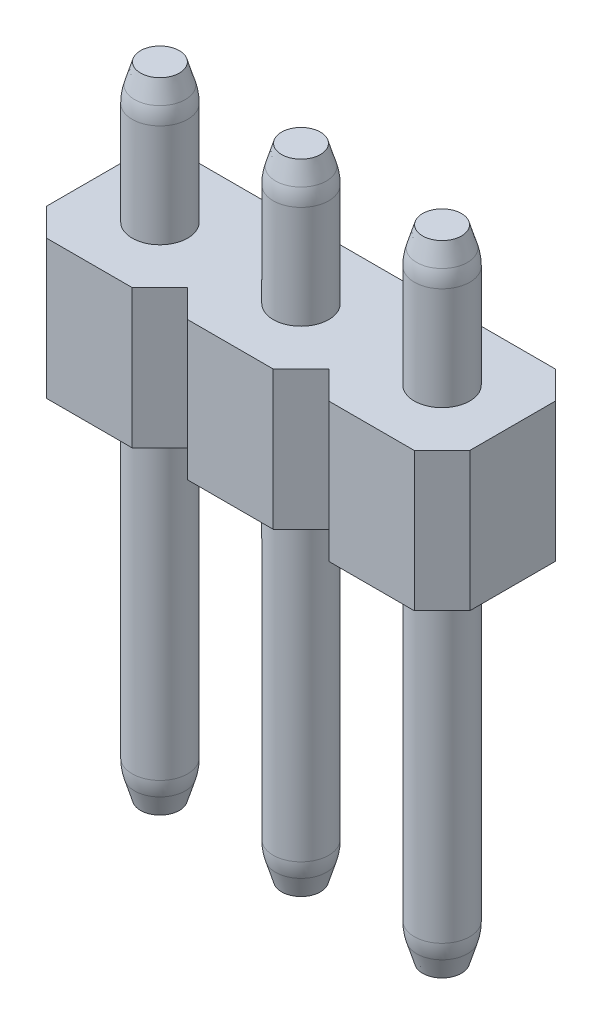
SolidWorks part; units mm, degrees
material "Brass"
ref_plane "Front Plane" through (0, 0, 0) normal (0, 0, 1) x (1, 0, 0)
ref_plane "Top Plane" through (0, 0, 0) normal (0, 1, 0) x (1, 0, 0)
ref_plane "Right Plane" through (0, 0, 0) normal (1, 0, 0) x (0, 0, -1)
sketch "Sketch1" plane through (0, 0, 0) normal (0, 1, 0) x (1, 0, 0)
  line L0 (0, 0) -> (2.54, 0) construction
  circle A0 centre (0, 0) radius 0.5
  circle A1 centre (2.54, 0) radius 0.5
  circle A2 centre (5.08, 0) radius 0.5
  circle A3 centre (7.62, 0) radius 0.5
  circle A4 centre (10.16, 0) radius 0.5
  circle A5 centre (12.7, 0) radius 0.5
  circle A6 centre (15.24, 0) radius 0.5
  circle A7 centre (17.78, 0) radius 0.5
  circle A8 centre (20.32, 0) radius 0.5
  circle A9 centre (22.86, 0) radius 0.5
  circle A10 centre (25.4, 0) radius 0.5
  circle A11 centre (27.94, 0) radius 0.5
  circle A12 centre (30.48, 0) radius 0.5
  circle A13 centre (33.02, 0) radius 0.5
  circle A14 centre (35.56, 0) radius 0.5
  circle A15 centre (38.1, 0) radius 0.5
  dimension "D1" = 1
  dimension "D3" = 2.54
  dimension "D2" = 16
extrude "Boss-Extrude1" add sketch "Sketch1" along normal blind 11.5
ref_plane "Plane1" through (0, 6.5, 0) normal (0, 1, 0) x (1, 0, 0)
sketch "Sketch2" plane through (0, 6.5, 0) normal (0, 1, 0) x (1, 0, 0)
  line L0 (-1.27, 0.77) -> (-0.77, 1.27)
  line L1 (-0.77, -1.27) -> (0.77, -1.27)
  line L2 (-1.27, -0.77) -> (-1.27, 0.77)
  line L3 (-0.77, 1.27) -> (0.77, 1.27)
  line L5 (-1.27, -1.27) -> (1.27, 1.27) construction
  line L6 (-1.27, 1.27) -> (1.27, -1.27) construction
  line L7 (0.77, 1.27) -> (1.27, 0.77)
  line L8 (0.77, -1.27) -> (1.27, -0.77)
  line L9 (-1.27, -0.77) -> (-0.77, -1.27)
  line L10 (1.27, 0.77) -> (1.77, 1.27)
  line L11 (1.77, 1.27) -> (3.31, 1.27)
  line L12 (3.31, 1.27) -> (3.81, 0.77)
  line L14 (3.31, -1.27) -> (3.81, -0.77)
  line L15 (1.77, -1.27) -> (3.31, -1.27)
  line L16 (1.27, -0.77) -> (1.77, -1.27)
  line L17 (3.81, 0.77) -> (4.31, 1.27)
  line L18 (4.31, 1.27) -> (5.85, 1.27)
  line L19 (5.85, 1.27) -> (6.35, 0.77)
  line L20 (6.35, -0.77) -> (6.35, 0.77) construction
  line L21 (5.85, -1.27) -> (6.35, -0.77)
  line L22 (4.31, -1.27) -> (5.85, -1.27)
  line L23 (3.81, -0.77) -> (4.31, -1.27)
  line L24 (6.35, 0.77) -> (6.85, 1.27)
  line L25 (6.85, 1.27) -> (8.39, 1.27)
  line L26 (8.39, 1.27) -> (8.89, 0.77)
  line L27 (8.89, -0.77) -> (8.89, 0.77) construction
  line L28 (8.39, -1.27) -> (8.89, -0.77)
  line L29 (6.85, -1.27) -> (8.39, -1.27)
  line L30 (6.35, -0.77) -> (6.85, -1.27)
  line L31 (8.89, 0.77) -> (9.39, 1.27)
  line L32 (9.39, 1.27) -> (10.93, 1.27)
  line L33 (10.93, 1.27) -> (11.43, 0.77)
  line L34 (11.43, -0.77) -> (11.43, 0.77) construction
  line L35 (10.93, -1.27) -> (11.43, -0.77)
  line L36 (9.39, -1.27) -> (10.93, -1.27)
  line L37 (8.89, -0.77) -> (9.39, -1.27)
  line L38 (11.43, 0.77) -> (11.93, 1.27)
  line L39 (11.93, 1.27) -> (13.47, 1.27)
  line L40 (13.47, 1.27) -> (13.97, 0.77)
  line L41 (13.97, -0.77) -> (13.97, 0.77) construction
  line L42 (13.47, -1.27) -> (13.97, -0.77)
  line L43 (11.93, -1.27) -> (13.47, -1.27)
  line L44 (11.43, -0.77) -> (11.93, -1.27)
  line L45 (13.97, 0.77) -> (14.47, 1.27)
  line L46 (14.47, 1.27) -> (16.01, 1.27)
  line L47 (16.01, 1.27) -> (16.51, 0.77)
  line L48 (16.51, -0.77) -> (16.51, 0.77) construction
  line L49 (16.01, -1.27) -> (16.51, -0.77)
  line L50 (14.47, -1.27) -> (16.01, -1.27)
  line L51 (13.97, -0.77) -> (14.47, -1.27)
  line L52 (16.51, 0.77) -> (17.01, 1.27)
  line L53 (17.01, 1.27) -> (18.55, 1.27)
  line L54 (18.55, 1.27) -> (19.05, 0.77)
  line L55 (19.05, -0.77) -> (19.05, 0.77) construction
  line L56 (18.55, -1.27) -> (19.05, -0.77)
  line L57 (17.01, -1.27) -> (18.55, -1.27)
  line L58 (16.51, -0.77) -> (17.01, -1.27)
  line L59 (19.05, 0.77) -> (19.55, 1.27)
  line L60 (19.55, 1.27) -> (21.09, 1.27)
  line L61 (21.09, 1.27) -> (21.59, 0.77)
  line L62 (21.59, -0.77) -> (21.59, 0.77) construction
  line L63 (21.09, -1.27) -> (21.59, -0.77)
  line L64 (19.55, -1.27) -> (21.09, -1.27)
  line L65 (19.05, -0.77) -> (19.55, -1.27)
  line L66 (21.59, 0.77) -> (22.09, 1.27)
  line L67 (22.09, 1.27) -> (23.63, 1.27)
  line L68 (23.63, 1.27) -> (24.13, 0.77)
  line L69 (24.13, -0.77) -> (24.13, 0.77) construction
  line L70 (23.63, -1.27) -> (24.13, -0.77)
  line L71 (22.09, -1.27) -> (23.63, -1.27)
  line L72 (21.59, -0.77) -> (22.09, -1.27)
  line L73 (24.13, 0.77) -> (24.63, 1.27)
  line L74 (24.63, 1.27) -> (26.17, 1.27)
  line L75 (26.17, 1.27) -> (26.67, 0.77)
  line L76 (26.67, -0.77) -> (26.67, 0.77) construction
  line L77 (26.17, -1.27) -> (26.67, -0.77)
  line L78 (24.63, -1.27) -> (26.17, -1.27)
  line L79 (24.13, -0.77) -> (24.63, -1.27)
  line L80 (26.67, 0.77) -> (27.17, 1.27)
  line L81 (27.17, 1.27) -> (28.71, 1.27)
  line L82 (28.71, 1.27) -> (29.21, 0.77)
  line L83 (29.21, -0.77) -> (29.21, 0.77) construction
  line L84 (28.71, -1.27) -> (29.21, -0.77)
  line L85 (27.17, -1.27) -> (28.71, -1.27)
  line L86 (26.67, -0.77) -> (27.17, -1.27)
  line L87 (29.21, 0.77) -> (29.71, 1.27)
  line L88 (29.71, 1.27) -> (31.25, 1.27)
  line L89 (31.25, 1.27) -> (31.75, 0.77)
  line L90 (31.75, -0.77) -> (31.75, 0.77) construction
  line L91 (31.25, -1.27) -> (31.75, -0.77)
  line L92 (29.71, -1.27) -> (31.25, -1.27)
  line L93 (29.21, -0.77) -> (29.71, -1.27)
  line L94 (31.75, 0.77) -> (32.25, 1.27)
  line L95 (32.25, 1.27) -> (33.79, 1.27)
  line L96 (33.79, 1.27) -> (34.29, 0.77)
  line L97 (34.29, -0.77) -> (34.29, 0.77) construction
  line L98 (33.79, -1.27) -> (34.29, -0.77)
  line L99 (32.25, -1.27) -> (33.79, -1.27)
  line L100 (31.75, -0.77) -> (32.25, -1.27)
  line L101 (34.29, 0.77) -> (34.79, 1.27)
  line L102 (34.79, 1.27) -> (36.33, 1.27)
  line L103 (36.33, 1.27) -> (36.83, 0.77)
  line L104 (36.83, -0.77) -> (36.83, 0.77) construction
  line L105 (36.33, -1.27) -> (36.83, -0.77)
  line L106 (34.79, -1.27) -> (36.33, -1.27)
  line L107 (34.29, -0.77) -> (34.79, -1.27)
  line L108 (36.83, 0.77) -> (37.33, 1.27)
  line L109 (37.33, 1.27) -> (38.87, 1.27)
  line L110 (38.87, 1.27) -> (39.37, 0.77)
  line L111 (39.37, -0.77) -> (39.37, 0.77)
  line L112 (38.87, -1.27) -> (39.37, -0.77)
  line L113 (37.33, -1.27) -> (38.87, -1.27)
  line L114 (36.83, -0.77) -> (37.33, -1.27)
  line L115 (-1.27, 0.77) -> (1.27, 0.77) construction
  point P0 (0, 0)
  dimension "D1" = 2.54
  dimension "D2" = 2.54
  dimension "D4" = 2.54
  dimension "D3" = 16
extrude "Boss-Extrude2" add sketch "Sketch2" along normal blind 2.5
chamfer "Chamfer1" distance 0.5 distance2 0.15 16 edges at (15.24, 11.5, 0.5) (12.7, 11.5, 0.5) (10.16, 11.5, 0.5) (7.62, 11.5, 0.5) (5.08, 11.5, 0.5) (2.54, 11.5, 0.5) (0, 11.5, 0.5) (38.1, 11.5, 0.5) (35.56, 11.5, 0.5) (33.02, 11.5, 0.5) (30.48, 11.5, 0.5) (27.94, 11.5, 0.5) (25.4, 11.5, 0.5) (22.86, 11.5, 0.5) (20.32, 11.5, 0.5) (17.78, 11.5, 0.5)
fillet "Fillet1" radius 1 16 edges at (38.1, 11, 0.5) (35.56, 11, 0.5) (33.02, 11, 0.5) (30.48, 11, 0.5) (27.94, 11, 0.5) (25.4, 11, 0.5) (22.86, 11, 0.5) (20.32, 11, 0.5) (17.78, 11, 0.5) (15.24, 11, 0.5) (12.7, 11, 0.5) (10.16, 11, 0.5) (7.62, 11, 0.5) (5.08, 11, 0.5) (2.54, 11, 0.5) (0, 11, 0.5)
chamfer "Chamfer2" distance 0.15 distance2 0.5 16 edges at (10.16, 0, 0.5) (17.78, 0, 0.5) (22.86, 0, 0.5) (27.94, 0, 0.5) (30.48, 0, 0.5) (0, 0, 0.5) (2.54, 0, 0.5) (5.08, 0, 0.5) (7.62, 0, 0.5) (12.7, 0, 0.5) (15.24, 0, 0.5) (20.32, 0, 0.5) (25.4, 0, 0.5) (33.02, 0, 0.5) (35.56, 0, 0.5) (38.1, 0, 0.5)
fillet "Fillet2" radius 1 16 edges at (30.48, 0.5, 0.5) (33.02, 0.5, 0.5) (35.56, 0.5, 0.5) (38.1, 0.5, 0.5) (27.94, 0.5, 0.5) (25.4, 0.5, 0.5) (22.86, 0.5, 0.5) (20.32, 0.5, 0.5) (17.78, 0.5, 0.5) (15.24, 0.5, 0.5) (12.7, 0.5, 0.5) (10.16, 0.5, 0.5) (7.62, 0.5, 0.5) (5.08, 0.5, 0.5) (2.54, 0.5, 0.5) (0, 0.5, 0.5)
sketch "Sketch3" plane through (0, 0, -1.27) normal (0, 0, -1) x (-1, 0, 0)
  line L0 (-31.75, 9) -> (-31.75, 6.5) construction
  line L1 (-31.75, 11.5) -> (-31.75, 0)
  line L2 (-24.13, 9) -> (-24.13, 6.5) construction
  line L3 (-24.13, 11.5) -> (-24.13, 0)
  line L4 (-31.75, 0) -> (-40.2825, 0)
  line L5 (-40.2825, 0) -> (-40.2825, 14.7026)
  line L6 (-40.2825, 14.7026) -> (-31.75, 11.5)
  line L7 (-24.13, 11.5) -> (2.3615, 11.5)
  line L8 (2.3615, 11.5) -> (2.4072, -1.428)
  line L9 (2.4072, -1.428) -> (-24.13, 0)
extrude "Cut-Extrude1" cut sketch "Sketch3" against normal through all both and the other way through all
